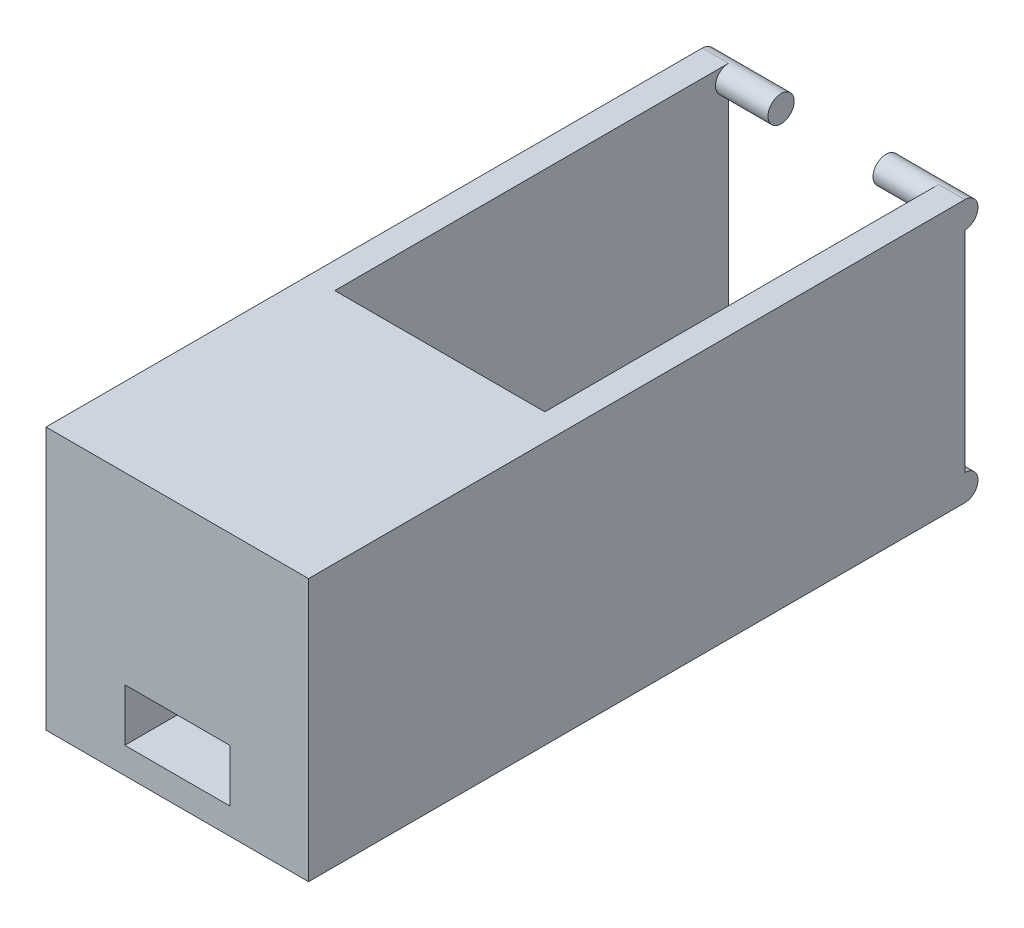
SolidWorks part; units mm, degrees
ref_plane "Front" through (0, 0, 0) normal (0, 0, 1) x (1, 0, 0)
ref_plane "Top" through (0, 0, 0) normal (0, 1, 0) x (1, 0, 0)
ref_plane "Right" through (0, 0, 0) normal (1, 0, 0) x (0, 0, -1)
sketch "草图1" plane through (0, 0, 0) normal (0, 1, 0) x (1, 0, 0)
  line L1 (-10, 30) -> (10, 30)
  line L2 (-10, 30) -> (-10, -20)
  line L3 (-10, -20) -> (10, -20)
  line L4 (10, 30) -> (10, -20)
  dimension "D1" = 50
  dimension "D2" = 20
  dimension "D3" = 10
  dimension "D4" = 20
extrude "凸台-拉伸1" add sketch "草图1" along normal blind 20
sketch "草图2" plane through (0, 20, 0) normal (0, 1, 0) x (1, 0, 0)
  line L0 (10, 30) -> (-10, 30) construction
  line L1 (-8, 30) -> (8, 30)
  line L2 (-8, 30) -> (-8, 0)
  line L3 (-8, 0) -> (8, 0)
  line L4 (8, 30) -> (8, 0)
  dimension "D1" = 16
  dimension "D2" = 8
extrude "切除-拉伸1" cut sketch "草图2" against normal blind 18
sketch "草图3" plane through (0, 0, 0) normal (0, -1, 0) x (1, 0, 0)
  line L0 (10, -30) -> (-10, -30) construction
  line L1 (-4, -42.4027) -> (4, -42.4027)
  line L2 (-4, -42.4027) -> (-4, -4)
  line L3 (-4, -4) -> (4, -4)
  line L4 (4, -42.4027) -> (4, -4)
  dimension "D1" = 8
  dimension "D2" = 4
  dimension "D3" = 26
extrude "切除-拉伸2" cut sketch "草图3" against normal blind 18
sketch "草图4" plane through (-4, 0, 0) normal (1, 0, 0) x (0, 0, -1)
  line L0 (30, 2) -> (30, 0) construction
  line L1 (30, 20) -> (30, 0) construction
  circle A0 centre (30, 1) radius 1
  circle A1 centre (30, 19) radius 1
extrude "凸台-拉伸2" add sketch "草图4" against normal blind 6
sketch "草图5" plane through (4, 0, 0) normal (-1, 0, 0) x (0, 0, 1)
  line L0 (-30, 0) -> (-30, 2) construction
  circle A0 centre (-30, 1) radius 1
  circle A1 centre (-30, 19) radius 1
extrude "凸台-拉伸3" add sketch "草图5" against normal blind 6
sketch "草图6" plane through (0, 0, 0) normal (0, 0, -1) x (-1, 0, 0)
  line L1 (-4, 2) -> (4, 2)
  line L2 (-4, 2) -> (-4, 6)
  line L3 (-4, 6) -> (4, 6)
  line L4 (4, 2) -> (4, 6)
  dimension "D1" = 8
  dimension "D2" = 4
extrude "切除-拉伸3" cut sketch "草图6" against normal blind 30
